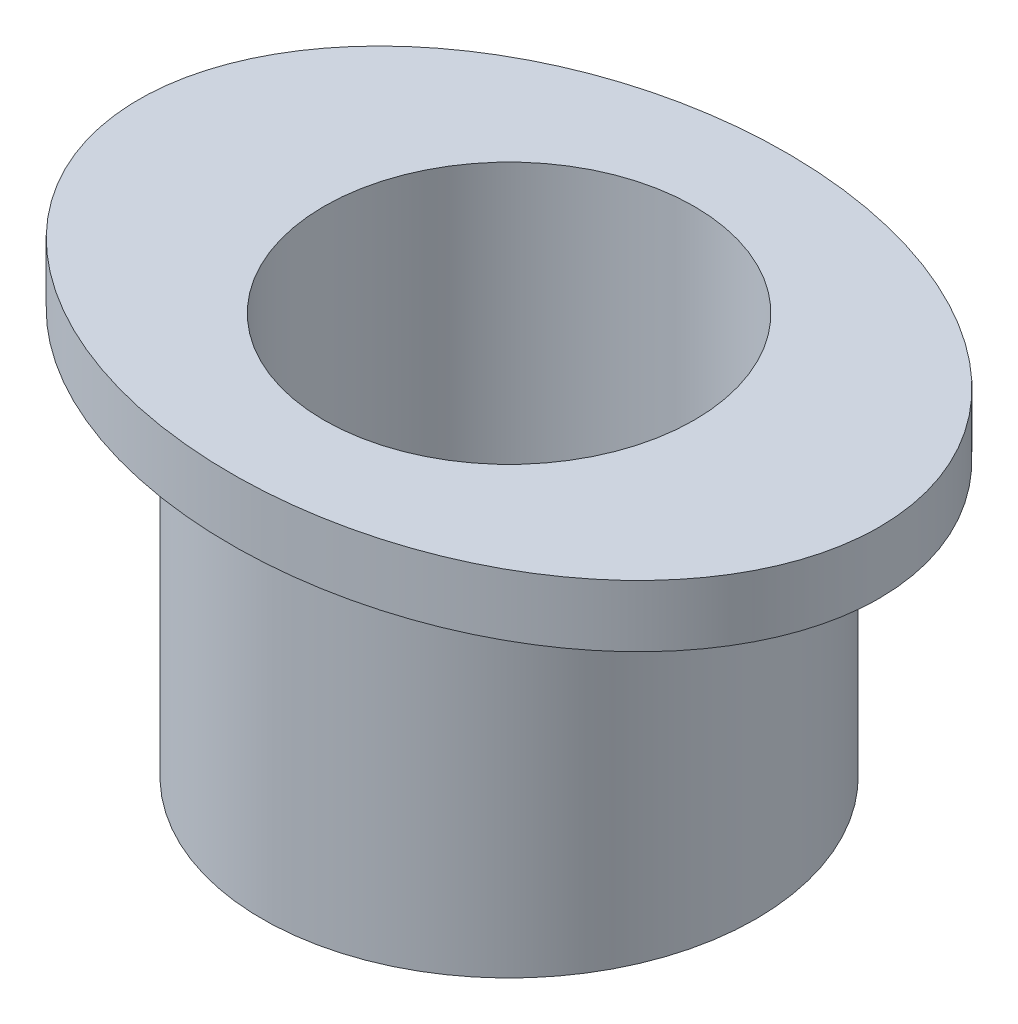
SolidWorks part; units mm, degrees
material "ABS"
ref_plane "Front Plane" through (0, 0, 0) normal (0, 0, 1) x (1, 0, 0)
ref_plane "Top Plane" through (0, 0, 0) normal (0, 1, 0) x (1, 0, 0)
ref_plane "Right Plane" through (0, 0, 0) normal (1, 0, 0) x (0, 0, -1)
sketch "Sketch1" plane through (0, 0, 0) normal (0, 1, 0) x (1, 0, 0)
  circle A0 centre (0, 0) radius 3
  dimension "D1" = 6
extrude "Extrude-Thin1" add sketch "Sketch1" against normal blind 5.5 thin
sketch "Sketch2" plane through (0, 0, 0) normal (0, 1, 0) x (1, 0, 0)
  line L0 (0, 4.5) -> (0, -4.5) construction
  line L1 (-6, 0) -> (6, 0) construction
  circle A0 centre (0, 0) radius 3
  circle A1 centre (0, 0) radius 3 construction
  ellipse E0 centre (0, 0) end of major axis (6, 0) minor radius 4.5
  dimension "D1" = 9
  dimension "D2" = 12
extrude "Boss-Extrude1" add sketch "Sketch2" along normal blind 1
